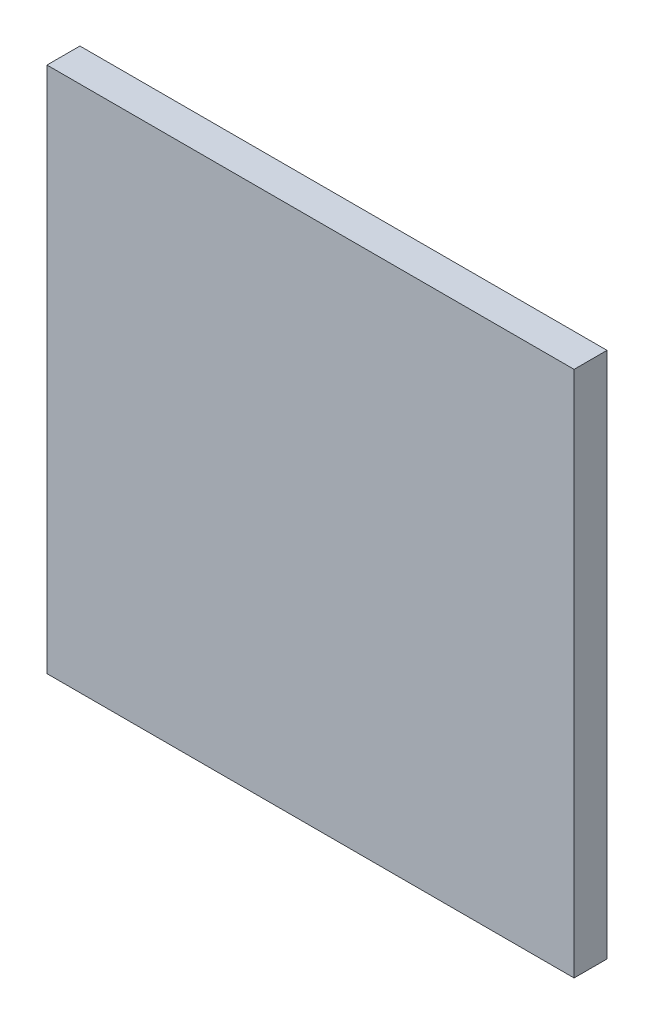
SolidWorks part; units mm, degrees
ref_plane "Front Plane" through (0, 0, 0) normal (0, 0, 1) x (1, 0, 0)
ref_plane "Top Plane" through (0, 0, 0) normal (0, 1, 0) x (1, 0, 0)
ref_plane "Right Plane" through (0, 0, 0) normal (1, 0, 0) x (0, 0, -1)
sketch "Sketch1" plane through (0, 0, 0) normal (0, 0, 1) x (1, 0, 0)
  line L1 (-20, -20) -> (20, -20)
  line L2 (-20, -20) -> (-20, 20)
  line L3 (-20, 20) -> (20, 20)
  line L4 (20, -20) -> (20, 20)
  line L5 (-20, -20) -> (20, 20) construction
  line L6 (-20, 20) -> (20, -20) construction
  point P0 (0, 0)
  dimension "D1" = 40
extrude "Boss-Extrude1" add sketch "Sketch1" along normal blind 2.5
